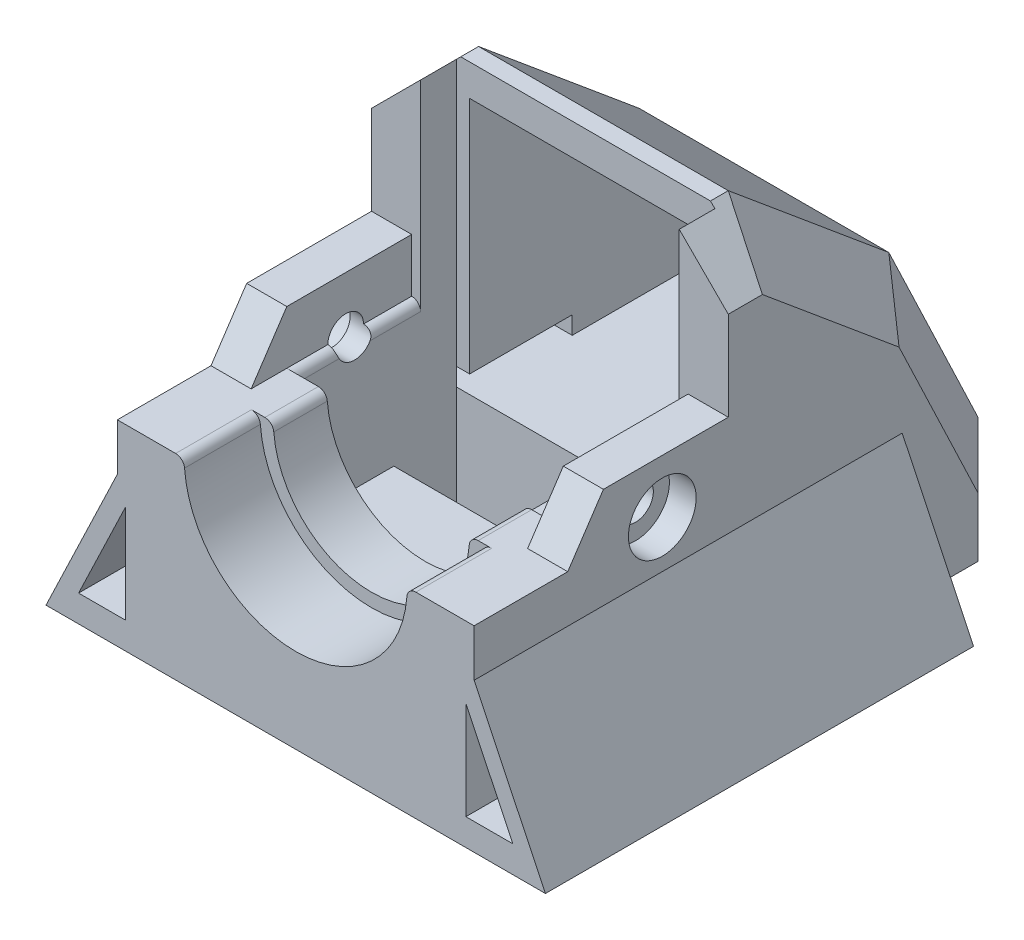
SolidWorks part; units mm, degrees
ref_plane "Ebene vorne" through (0, 0, 0) normal (0, 0, 1) x (1, 0, 0)
ref_plane "Ebene oben" through (0, 0, 0) normal (0, 1, 0) x (1, 0, 0)
ref_plane "Ebene rechts" through (0, 0, 0) normal (1, 0, 0) x (0, 0, -1)
sketch "Skizze1" plane through (0, 0, 0) normal (0, 0, 1) x (1, 0, 0)
  line L1 (0, 0) -> (20, 0)
  line L2 (0, 0) -> (0, 22)
  line L3 (0, 22) -> (20, 22)
  line L4 (20, 0) -> (20, 22)
  dimension "D1" = 22
  dimension "D2" = 20
extrude "Aufsatz-Linear austragen1" add sketch "Skizze1" along normal blind 35
sketch "Skizze2" plane through (0, 0, 35) normal (0, 0, 1) x (1, 0, 0)
  line L0 (0, 22) -> (0, 0) construction
  line L1 (20, 22) -> (0, 22) construction
  circle A0 centre (10, 11) radius 5.5
  dimension "D3" = 11
  dimension "D1" = 10
  dimension "D2" = 11
extrude "Schnitt-Linear austragen1" cut sketch "Skizze2" against normal blind 11
sketch "Skizze3" plane through (0, 0, 35) normal (0, 0, 1) x (1, 0, 0)
  line L0 (20, 0) -> (20, 22) construction
  line L1 (20, 22) -> (0, 22) construction
  circle A0 centre (10, 11) radius 6.25
  dimension "D1" = 10
  dimension "D2" = 11
extrude "Schnitt-Linear austragen2" cut sketch "Skizze3" against normal blind 8
sketch "Skizze5" plane through (0, 0, 24) normal (0, 0, 1) x (1, 0, 0)
  line L0 (0, 22) -> (0, 0) construction
  line L1 (2.75, 3.75) -> (17.25, 3.75)
  line L2 (2.75, 3.75) -> (2.75, 22)
  line L3 (2.75, 22) -> (17.25, 22)
  line L4 (17.25, 3.75) -> (17.25, 22)
  line L6 (0, 0) -> (20, 0) construction
  dimension "D1" = 18.25
  dimension "D2" = 14.5
  dimension "D3" = 2.75
  dimension "D4" = 3.75
extrude "Schnitt-Linear austragen3" cut sketch "Skizze5" against normal blind 9
sketch "Skizze13" plane through (0, 0, 35) normal (0, 0, 1) x (1, 0, 0)
  line L0 (20, 0) -> (20, 22) construction
  line L1 (0, 22) -> (20, 22)
  line L2 (0, 22) -> (0, 11)
  line L3 (0, 11) -> (20, 11)
  line L4 (20, 22) -> (20, 11)
extrude "Schnitt-Linear austragen6" cut sketch "Skizze13" against normal blind 18
sketch "Skizze16" plane through (0, 0, 0) normal (-1, 0, 0) x (0, 0, 1)
  line L0 (14, 22) -> (5, 14.5)
  line L1 (17, 22) -> (0, 22) construction
  line L2 (5, 14.5) -> (0, 4)
  line L3 (0, 22) -> (0, 0) construction
  line L4 (0, 4) -> (0, 22)
  line L5 (0, 22) -> (14, 22)
  line L6 (17, 22) -> (17, 11) construction
  dimension "D1" = 3
  dimension "D2" = 5
  dimension "D3" = 18
  dimension "D4" = 10.5
extrude "Schnitt-Linear austragen7" cut sketch "Skizze16" against normal through all
fillet "Verrundung1" radius 0.5 6 edges at (16.25, 11, 31) (3.75, 11, 31) (15.5, 11, 25.5) (4.5, 11, 25.5) (17.25, 11, 20.5) (2.75, 11, 20.5)
chamfer "Fase1" distance 3 angle 45 2 edges at (20, 22, 15.5) (0, 22, 15.5)
chamfer "Fase2" distance 3 angle 45 2 edges at (0, 16.75, 7.7) (20, 16.75, 7.7)
chamfer "Fase3" distance 3 angle 45 4 edges at (20, 6.0129, 0.9585) (20, 2, 0) (0, 6.0129, 0.9585) (0, 2, 0)
chamfer "Fase4" distance 1.5 angle 45 2 edges at (20, 11, 26) (0, 11, 26)
sketch "Skizze17" plane through (0, 3.75, 0) normal (0, 1, 0) x (1, 0, 0)
  line L1 (2.75, -15) -> (8.75, -15)
  line L2 (2.75, -15) -> (2.75, -18.5)
  line L3 (2.75, -18.5) -> (8.75, -18.5)
  line L4 (8.75, -15) -> (8.75, -18.5)
  dimension "D1" = 6
  dimension "D2" = 3.5
extrude "Schnitt-Linear austragen8" cut sketch "Skizze17" against normal through all
sketch "Skizze18" plane through (0, 0, 0) normal (-1, 0, 0) x (0, 0, 1)
  line L0 (17, 11) -> (35, 11) construction
  line L1 (35, 0) -> (31.25, 0)
  line L2 (35, 0) -> (35, 11)
  line L3 (35, 11) -> (31.25, 11)
  line L4 (31.25, 0) -> (31.25, 11)
  dimension "D1" = 3.75
extrude "Schnitt-Linear austragen9" cut sketch "Skizze18" against normal up to surface (20 mm away) up to face at (20, 9.1173, 16.564)
ref_plane "Ebene1" through (10, 0, 0) normal (-1, 0, 0) x (0, 0, 1)
sketch "Skizze22" plane through (10, 0, 0) normal (-1, 0, 0) x (0, 0, 1)
  line L0 (15, 20.2299) -> (6.6172, 13.2443)
  line L1 (15, 3.75) -> (15, 21.75) construction
  line L2 (7.4258, 12.6164) -> (5, 14.5) construction
  line L3 (6.6172, 13.2443) -> (5.76, 11.8961)
  line L4 (5.76, 11.8961) -> (3.76, 11.8961)
  line L5 (5, 14.5) -> (0, 4) construction
  line L6 (3.76, 11.8961) -> (0.8806, 5.8493)
  line L7 (0.8806, 5.8493) -> (6.0352, 5.8493)
  line L8 (6.0352, 5.8493) -> (15, 5.8493)
  line L9 (15, 5.8493) -> (15, 20.2299)
  line L10 (14, 22) -> (5, 14.5) construction
  dimension "D1" = 2
  dimension "D2" = 2
extrude "Schnitt-Linear austragen10" cut sketch "Skizze22" against normal blind 6.5 and the other way blind 6.5
sketch "Skizze23" plane through (0, 0, 31.25) normal (0, 0, 1) x (1, 0, 0)
  line L0 (0, 8.353) -> (-4, 0)
  line L1 (-4, 0) -> (0, 0)
  line L2 (0, 0) -> (0, 8.353)
  dimension "D1" = 4
extrude "Aufsatz-Linear austragen2" add sketch "Skizze23" against normal blind 24
mirror "Spiegeln1" about plane through (10, 0, 0) normal (-1, 0, 0) of "Aufsatz-Linear austragen2"
sketch "Skizze24" plane through (0, 0, 31.25) normal (0, 0, 1) x (1, 0, 0)
  line L0 (0.4608, 1.5) -> (-2.173, 1.5)
  line L1 (-2.173, 1.5) -> (0.4608, 7)
  line L2 (0.4608, 7) -> (0.4608, 1.5)
  line L3 (0, 8.353) -> (-4, 0) construction
  line L4 (24, 0) -> (-4, 0) construction
  dimension "D1" = 1
  dimension "D2" = 1.5
  dimension "D3" = 5.5
extrude "Schnitt-Linear austragen11" cut sketch "Skizze24" against normal blind 22
sketch "Skizze26" plane through (16.5, 0, 0) normal (-1, 0, 0) x (0, 0, 1)
  line L1 (15, 5.8493) -> (9.25, 5.8493)
  line L2 (15, 5.8493) -> (15, 6.8493)
  line L3 (15, 6.8493) -> (9.25, 6.8493)
  line L4 (9.25, 5.8493) -> (9.25, 6.8493)
  dimension "D1" = 5.75
  dimension "D2" = 1
extrude "Schnitt-Linear austragen12" cut sketch "Skizze26" against normal blind 4
mirror "Spiegeln2" about plane through (10, 0, 0) normal (-1, 0, 0) of "Schnitt-Linear austragen12"
mirror "Spiegeln3" about plane through (10, 0, 0) normal (-1, 0, 0) of "Schnitt-Linear austragen11"
sketch "Skizze27" plane through (0, 0, 17) normal (0, 0, 1) x (1, 0, 0)
  line L0 (0, 9.5) -> (1.5, 11)
  line L1 (1.5, 11) -> (0, 11)
  line L2 (0, 19) -> (0, 9.5) construction
  line L3 (0, 11) -> (0, 9.5)
extrude "Aufsatz-Linear austragen3" add sketch "Skizze27" along normal up to surface (14.25 mm away) up to face at (10, 7.9324, 31.25)
mirror "Spiegeln4" about plane through (10, 0, 0) normal (-1, 0, 0) of "Aufsatz-Linear austragen3"
sketch "Skizze28" plane through (0, 0, 17) normal (0, 0, 1) x (1, 0, 0)
  line L5 (0, 19) -> (0, 11) construction
  line L6 (2.25, 11) -> (0, 11)
  line L7 (2.25, 11) -> (2.25, 14)
  line L8 (2.25, 14) -> (0, 14)
  line L9 (0, 11) -> (0, 14)
  dimension "D1" = 3
extrude "Aufsatz-Linear austragen4" add sketch "Skizze28" along normal up to surface (7 mm away) up to face at (10, 8.8943, 24)
sketch "Skizze31" plane through (0, 0, 0) normal (-1, 0, 0) x (0, 0, 1)
  line L0 (24, 14) -> (26, 11)
  line L1 (31.25, 11) -> (24, 11) construction
  line L2 (26, 11) -> (24, 11)
  line L3 (24, 11) -> (24, 14)
  dimension "D1" = 2
extrude "Aufsatz-Linear austragen6" add sketch "Skizze31" against normal up to surface (2.25 mm away) up to face at (2.25, 12.5, 20.5)
sketch "Skizze32" plane through (0, 0, 0) normal (-1, 0, 0) x (0, 0, 1)
  line L2 (31.25, 11) -> (26, 11) construction
  circle A0 centre (20.7, 11) radius 1
  dimension "D1" = 2
  dimension "D2" = 3.3
extrude "Schnitt-Linear austragen13" cut sketch "Skizze32" against normal up to surface (17.25 mm away)
sketch "Skizze33" plane through (10, 0, 0) normal (-1, 0, 0) x (0, 0, 1)
  circle A0 centre (20.7, 11) radius 1.9
  dimension "D1" = 3.8
extrude "Schnitt-Linear austragen14" cut sketch "Skizze33" against normal blind 1.5 from surface at 10 starting at face at (0, 11, 21.7)
mirror "Spiegeln6" about plane through (10, 0, 0) normal (-1, 0, 0) of "Aufsatz-Linear austragen6", "Aufsatz-Linear austragen4"
mirror "Spiegeln8" about plane through (10, 0, 0) normal (-1, 0, 0) of "Schnitt-Linear austragen13"
sketch "Skizze34" plane through (20, 0, 0) normal (1, 0, 0) x (0, 0, -1)
  circle A0 centre (-20.7, 11) radius 1.9
  dimension "D1" = 3.8
extrude "Schnitt-Linear austragen15" cut sketch "Skizze34" against normal blind 1.5
